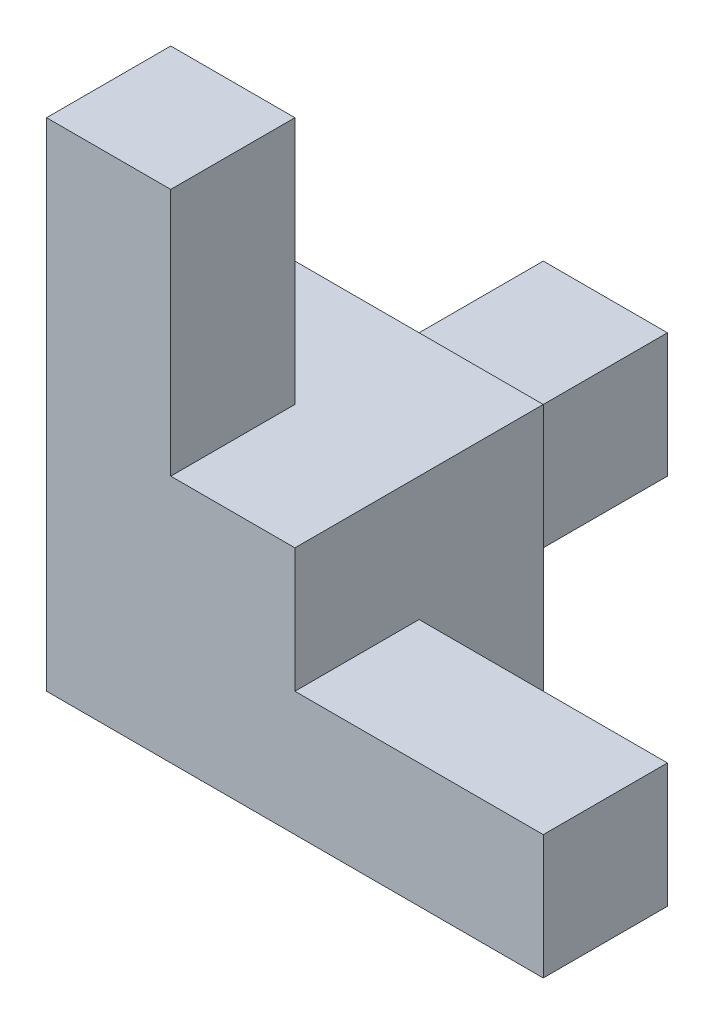
SolidWorks part; units mm, degrees
ref_plane "Front Plane" through (0, 0, 0) normal (0, 0, 1) x (1, 0, 0)
ref_plane "Top Plane" through (0, 0, 0) normal (0, 1, 0) x (1, 0, 0)
ref_plane "Right Plane" through (0, 0, 0) normal (1, 0, 0) x (0, 0, -1)
sketch "Sketch1" plane through (0, 0, 0) normal (0, 0, 1) x (1, 0, 0)
  line L1 (0, 0) -> (10, 0)
  line L2 (0, 0) -> (0, 40)
  line L3 (0, 40) -> (10, 40)
  line L4 (10, 10) -> (10, 40)
  line L5 (10, 0) -> (40, 0)
  line L7 (10, 10) -> (40, 10)
  line L8 (40, 0) -> (40, 10)
  dimension "D1" = 40
  dimension "D2" = 10
  dimension "D3" = 10
  dimension "D4" = 40
extrude "Boss-Extrude1" add sketch "Sketch1" along normal blind 10
sketch "Sketch2" plane through (0, 0, 0) normal (0, 0, -1) x (-1, 0, 0)
  line L1 (0, 0) -> (-10, 0)
  line L2 (0, 0) -> (0, 10)
  line L3 (0, 10) -> (-10, 10)
  line L4 (-10, 0) -> (-10, 10)
extrude "Boss-Extrude2" add sketch "Sketch2" along normal blind 30
sketch "Sketch3" plane through (0, 0, 10) normal (0, 0, 1) x (1, 0, 0)
  line L1 (0, 0) -> (20, 0)
  line L2 (0, 0) -> (0, 20)
  line L3 (0, 20) -> (20, 20)
  line L4 (20, 0) -> (20, 20)
  dimension "D1" = 20
  dimension "D2" = 20
extrude "Boss-Extrude3" add sketch "Sketch3" against normal blind 20
